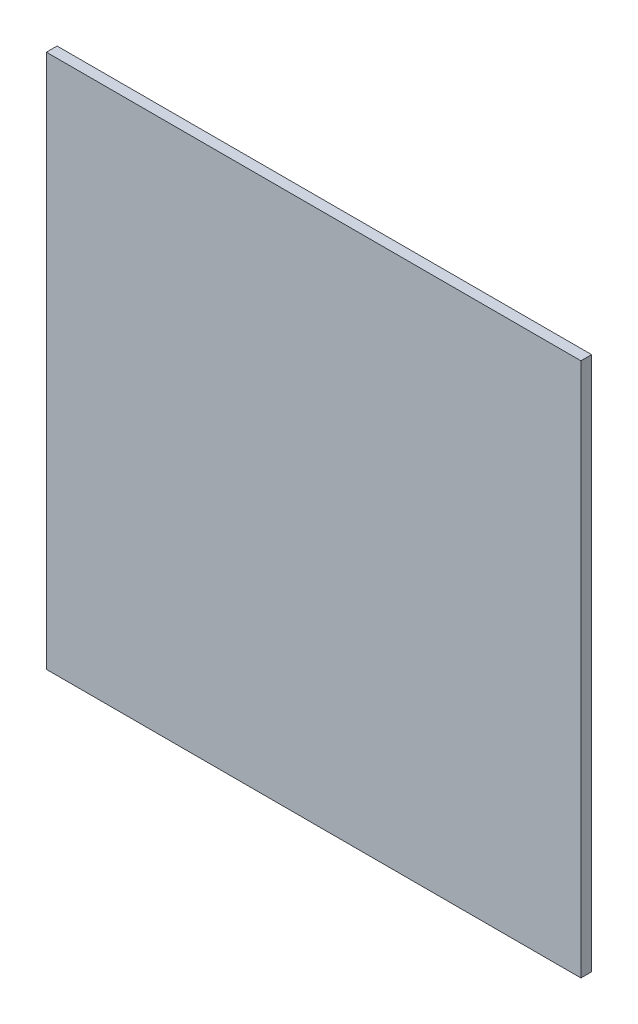
SolidWorks part; units mm, degrees
ref_plane "Front Plane" through (0, 0, 0) normal (0, 0, 1) x (1, 0, 0)
ref_plane "Top Plane" through (0, 0, 0) normal (0, 1, 0) x (1, 0, 0)
ref_plane "Right Plane" through (0, 0, 0) normal (1, 0, 0) x (0, 0, -1)
sketch "Sketch1" plane through (0, 0, 0) normal (0, 0, 1) x (1, 0, 0)
  line L1 (0, 0) -> (50, 0)
  line L2 (0, 0) -> (0, 50)
  line L3 (0, 50) -> (50, 50)
  line L4 (50, 0) -> (50, 50)
  dimension "D1" = 50
  dimension "D2" = 50
extrude "Boss-Extrude1" add sketch "Sketch1" along normal blind 1
